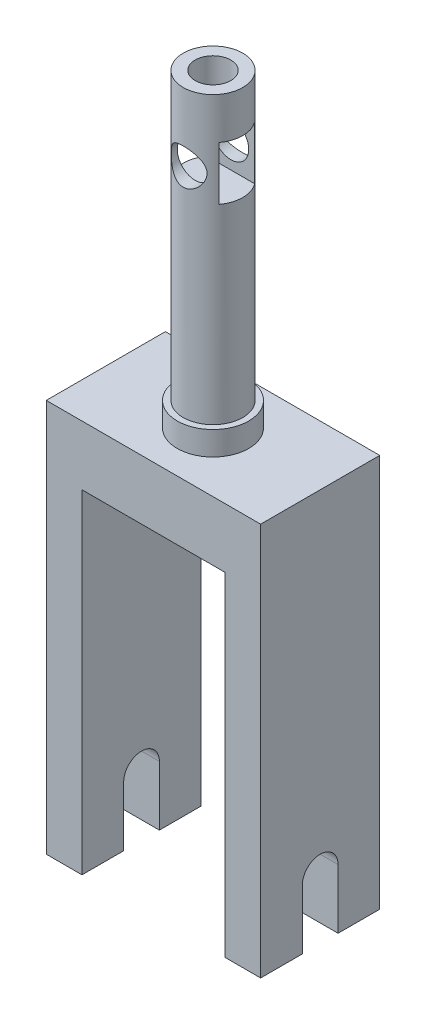
SolidWorks part; units mm, degrees
material "普通碳钢"
ref_plane "前视基准面" through (0, 0, 0) normal (0, 0, 1) x (1, 0, 0)
ref_plane "上视基准面" through (0, 0, 0) normal (0, 1, 0) x (1, 0, 0)
ref_plane "右视基准面" through (0, 0, 0) normal (1, 0, 0) x (0, 0, -1)
sketch "草图1" plane through (0, 0, 0) normal (0, 0, 1) x (1, 0, 0)
  line L0 (-15, -25.0867) -> (-15, 7.9133)
  line L1 (-15, 7.9133) -> (3, 7.9133)
  line L2 (3, 7.9133) -> (3, -25.0867)
  line L3 (3, -25.0867) -> (0, -25.0867)
  line L4 (0, -25.0867) -> (0, 2.9133)
  line L5 (0, 2.9133) -> (-12, 2.9133)
  line L6 (-12, 2.9133) -> (-12, -25.0867)
  line L7 (-12, -25.0867) -> (-15, -25.0867)
  dimension "D1" = 3
  dimension "D2" = 3
  dimension "D3" = 12
  dimension "D4" = 5
  dimension "D5" = 28
  dimension "D6" = 28
extrude "凸台-拉伸1" add sketch "草图1" along normal blind 10
sketch "草图2" plane through (3, 0, 0) normal (1, 0, 0) x (0, 0, -1)
  line L0 (-10, -25.0867) -> (0, -25.0867) construction
  line L1 (-10, -25.0867) -> (-10, 7.9133) construction
  line L2 (-6.5, -20.0867) -> (-6.5, -25.0867)
  line L3 (-6.5, -25.0867) -> (-3.5, -25.0867)
  line L4 (-3.5, -25.0867) -> (-3.5, -20.0867)
  arc A0 (-3.5, -20.0867) -> (-6.5, -20.0867) centre (-5, -20.0867) ccw
  dimension "D2" = 3
  dimension "D1" = 5
  dimension "D3" = 5
extrude "切除-拉伸1" cut sketch "草图2" against normal through all
sketch "草图9" plane through (0, 7.9133, 0) normal (0, 1, 0) x (1, 0, 0)
  line L0 (3, -10) -> (3, 0) construction
  line L1 (3, 0) -> (-15, 0) construction
  circle A0 centre (-6, -5) radius 3
  dimension "D1" = 9
  dimension "D3" = 6
  dimension "D2" = 5
extrude "凸台-拉伸2" add sketch "草图9" along normal blind 2
sketch "草图11" plane through (0, 9.9133, 0) normal (0, 1, 0) x (1, 0, 0)
  circle A0 centre (-6, -5) radius 2.5
  dimension "D1" = 5
extrude "凸台-拉伸4" add sketch "草图11" along normal blind 24
sketch "草图12" plane through (0, 0, 0) normal (1, 0, 0) x (0, 0, -1)
  line L1 (-6.5, 30.4133) -> (-3.5, 30.4133)
  line L2 (-6.5, 30.4133) -> (-6.5, 25.9133)
  line L3 (-6.5, 25.9133) -> (-3.5, 25.9133)
  line L4 (-3.5, 30.4133) -> (-3.5, 25.9133)
  dimension "D1" = 3
  dimension "D2" = 4.5
  dimension "D3" = 1.5
extrude "切除-拉伸2" cut sketch "草图12" against normal through all and the other way through all
sketch "草图13" plane through (0, 33.9133, 0) normal (0, 1, 0) x (-1, 0, 0)
  circle A0 centre (6, 5) radius 1.5
extrude "切除-拉伸3" cut sketch "草图13" against normal up to next
ref_plane "基准面1" through (0, 0, 5) normal (0, 0, 1) x (1, 0, 0)
sketch "草图15" plane through (0, 0, 5) normal (0, 0, 1) x (1, 0, 0)
  line L0 (-6, 34.7516) -> (-6, 24.6793) construction
  line L1 (-2.4786, 28.1633) -> (-9.8897, 28.1633) construction
  circle A0 centre (-6, 28.1633) radius 1.5
  point P4 (-6, 28.1633)
extrude "切除-拉伸4" cut sketch "草图15" against normal mid plane 10 contours A0
